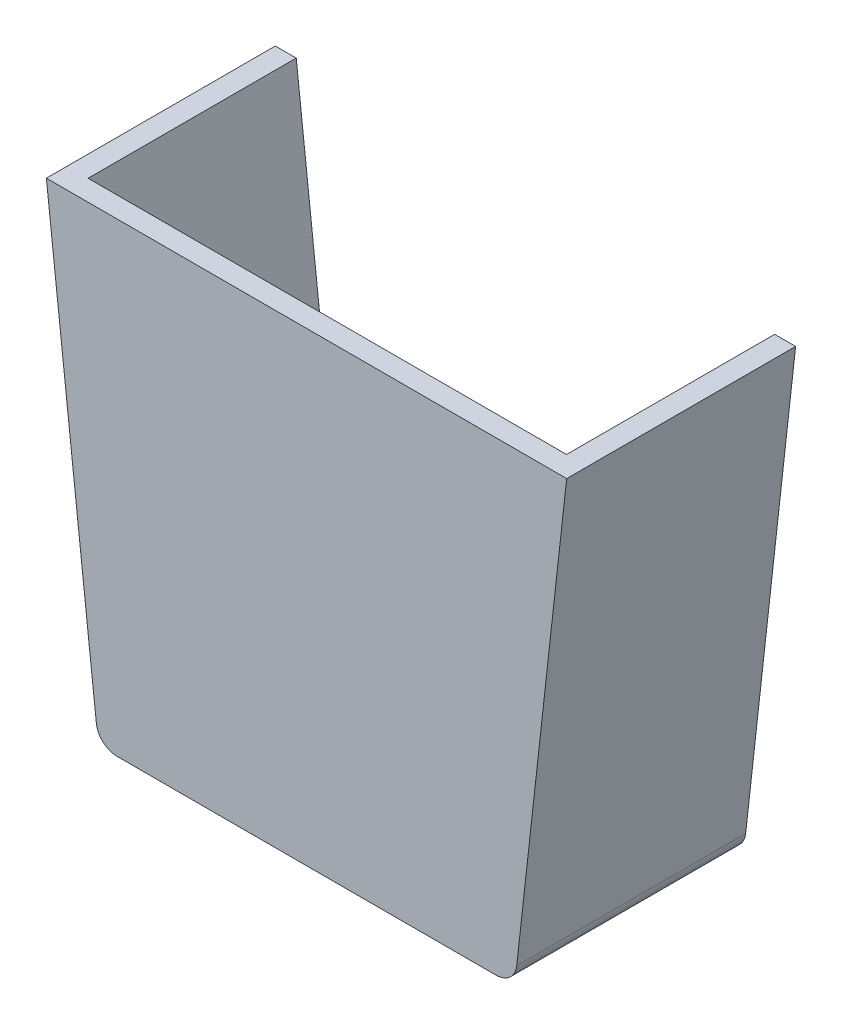
SolidWorks part; units mm, degrees
ref_plane "Front Plane" through (0, 0, 0) normal (0, 0, 1) x (1, 0, 0)
ref_plane "Top Plane" through (0, 0, 0) normal (0, 1, 0) x (1, 0, 0)
ref_plane "Right Plane" through (0, 0, 0) normal (1, 0, 0) x (0, 0, -1)
sketch "Sketch1" plane through (0, 0, 0) normal (0, 0, 1) x (1, 0, 0)
  line L0 (0, 56.7961) -> (0, -56.7961) construction
  line L1 (63.5, 56.7961) -> (-63.5, 56.7961)
  line L2 (-63.5, 56.7961) -> (-51.3049, -52.2806)
  line L3 (-46.2563, -56.7961) -> (46.2563, -56.7961)
  line L4 (63.5, 56.7961) -> (51.3049, -52.2806)
  arc A0 (-51.3049, -52.2806) -> (-46.2563, -56.7961) centre (-46.2563, -51.7161) ccw
  arc A1 (51.3049, -52.2806) -> (46.2563, -56.7961) centre (46.2563, -51.7161) cw
  circle A2 centre (0, 25.5165) radius 3.81
  circle A3 centre (0, -5.9961) radius 12.7
  point P10 (-50.8, -56.7961)
  dimension "D4" = 5.08
  dimension "D6" = 7.62
  dimension "D7" = 25.4
  dimension "D8" = 31.2797
  dimension "D9" = 50.8
  dimension "D1" = 50.8
  dimension "D2" = 63.5
  dimension "D3" = 56.7961
  dimension "D5" = 109.0767
extrude "Boss-Extrude1" add sketch "Sketch1" against normal blind 5.08 contours L0 L1 L2 A0 L3 A3 A2 | L1 L0 A2 A3 L3 A1 L4 | A3 L0 | L0 A3 | L0 A2 | A2 L0
sketch "Sketch2" plane through (0, 0, -5.08) normal (0, 0, 1) x (1, 0, 0)
  line L0 (0, 56.7961) -> (0, -56.7961) construction
  line L2 (-63.5, 56.7961) -> (-51.3049, -52.2806)
  line L3 (-46.2563, -56.7961) -> (46.2563, -56.7961)
  line L4 (63.5, 56.7961) -> (51.3049, -52.2806)
  line L5 (-46.2563, -56.7961) -> (46.2563, -56.7961) construction
  line L7 (58.3883, 56.7961) -> (46.7612, -47.2006)
  line L8 (41.7126, -51.7161) -> (-41.7126, -51.7161)
  line L9 (-58.3883, 56.7961) -> (-46.7612, -47.2006)
  line L10 (63.5, 56.7961) -> (-63.5, 56.7961) construction
  line L11 (63.5, 56.7961) -> (58.3883, 56.7961)
  line L12 (-58.3883, 56.7961) -> (-63.5, 56.7961)
  arc A0 (-51.3049, -52.2806) -> (-46.2563, -56.7961) centre (-46.2563, -51.7161) ccw
  arc A1 (51.3049, -52.2806) -> (46.2563, -56.7961) centre (46.2563, -51.7161) cw
  circle A2 centre (0, 26.1693) radius 3.81
  circle A3 centre (0, -32.9791) radius 12.7
  arc A4 (46.7612, -47.2006) -> (41.7126, -51.7161) centre (41.7126, -46.6361) cw
  arc A5 (-46.7612, -47.2006) -> (-41.7126, -51.7161) centre (-41.7126, -46.6361) ccw
  point P2 (0, 0)
  point P10 (-50.8, -56.7961)
  point P19 (0, 0)
  dimension "D4" = 5.08
  dimension "D6" = 7.62
  dimension "D7" = 25.4
  dimension "D8" = 104.6447
  dimension "D9" = 23.8171
  dimension "D11" = 5.08
  dimension "D3" = 54.6238
  dimension "D12" = 46.2563
  dimension "D2" = 63.5
  dimension "D5" = 109.0767
  dimension "D10" = 360
extrude "Boss-Extrude2" add sketch "Sketch2" against normal blind 50.8
